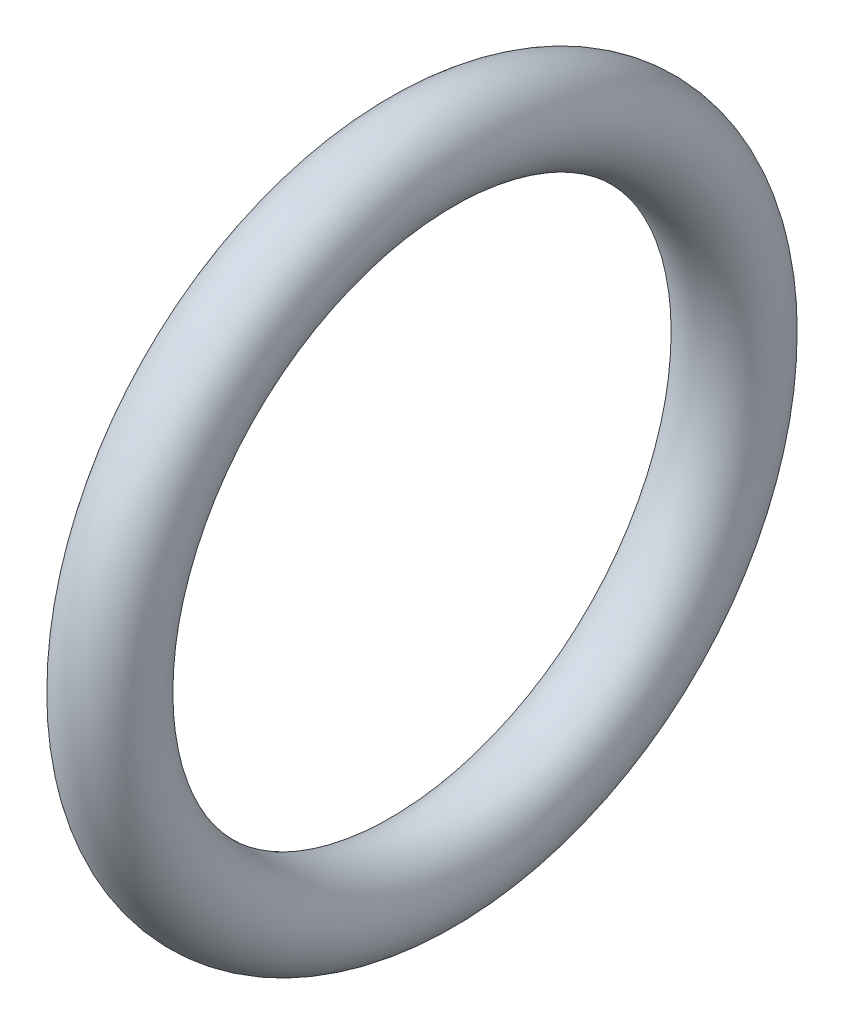
SolidWorks part; units mm, degrees
ref_plane "Front Plane" through (0, 0, 0) normal (0, 0, 1) x (1, 0, 0)
ref_plane "Top Plane" through (0, 0, 0) normal (0, 1, 0) x (1, 0, 0)
ref_plane "Right Plane" through (0, 0, 0) normal (1, 0, 0) x (0, 0, -1)
sketch "Sketch1" plane through (0, 0, 0) normal (0, 0, 1) x (1, 0, 0)
  circle A0 centre (0, 0) radius 4.7625 construction
  circle A1 centre (0, 0) radius 6.35 construction
  circle A2 centre (0, 5.5563) radius 0.7937
  dimension "D1" = 9.525
  dimension "D2" = 12.7
sketch "Sketch2" plane through (0, 0, 0) normal (0, 0, -1) x (-1, 0, 0)
  line L0 (3.1802, 0) -> (-2.626, 0) construction
revolve "Revolve2" add sketch "Sketch1" angle 360 about L0
split "Split1"
